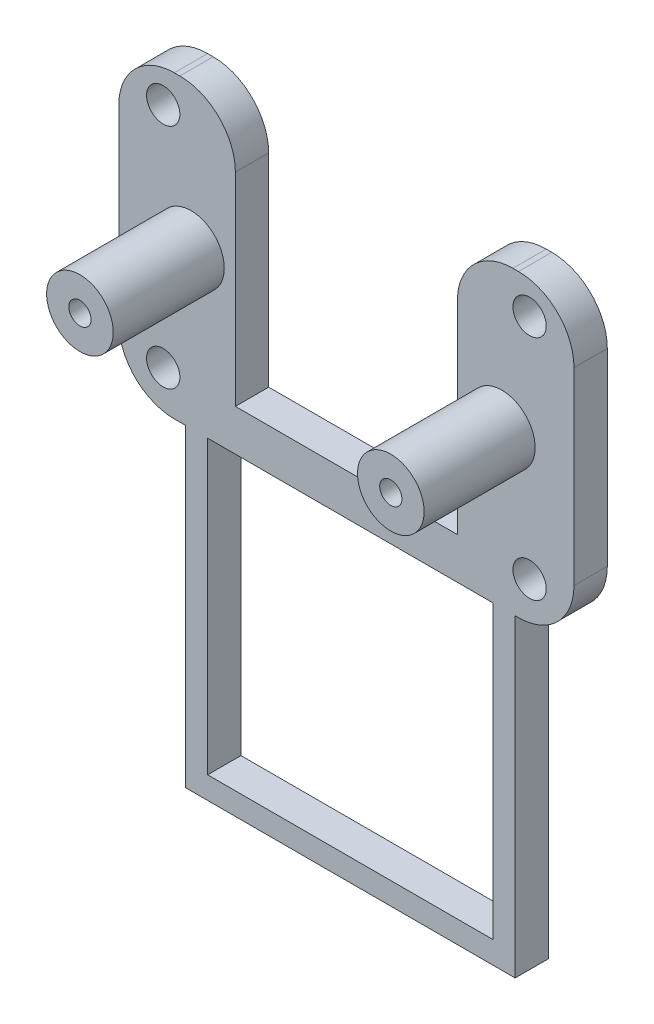
SolidWorks part; units mm, degrees
ref_plane "Plan de face" through (0, 0, 0) normal (0, 0, 1) x (1, 0, 0)
ref_plane "Plan de dessus" through (0, 0, 0) normal (0, 1, 0) x (1, 0, 0)
ref_plane "Plan de droite" through (0, 0, 0) normal (1, 0, 0) x (0, 0, -1)
sketch "Esquisse1" plane through (0, 0, 0) normal (0, 0, 1) x (1, 0, 0)
  line L0 (0, 0) -> (20.5, 0) construction
  line L1 (0, 0) -> (41, 0)
  line L2 (0, 0) -> (0, 27)
  line L3 (0, 27) -> (41, 27)
  line L4 (41, 0) -> (41, 27)
  line L5 (10.5, 3.7273) -> (30.5, 3.7273)
  line L6 (10.5, 3.7273) -> (10.5, 27.9545)
  line L7 (10.5, 27.9545) -> (30.5, 27.9545)
  line L8 (30.5, 3.7273) -> (30.5, 27.9545)
  line L9 (5.65, 0) -> (7.7004, 0)
  line L10 (5.65, 0) -> (35.35, 0)
  line L11 (7.65, 0) -> (33.35, 0)
  line L13 (7.65, 0) -> (33.35, 0)
  line L14 (7.65, 0) -> (16.0275, 0)
  line L17 (7.65, 0) -> (33.35, 0)
  line L23 (33.35, 0) -> (35.35, 0)
  line L24 (33.35, 0) -> (35.35, 0)
  circle A1 centre (4, 23.9981) radius 1.5
  circle A2 centre (4, 3.4981) radius 1.5
  circle A4 centre (37, 3.5002) radius 1.5
  circle A7 centre (37, 23.9983) radius 1.5
  dimension "D1" = 20.5
  dimension "D2" = 20.4981
  dimension "D3" = 33
  dimension "D5" = 3.5002
  dimension "D6" = 3.4981
  dimension "D7" = 10.5
  dimension "D9" = 20
extrude "Boss.-Extru.1" add sketch "Esquisse1" along normal blind 3 contours L8 L5 L6 L3 L2 L1 L4
sketch "Esquisse3" plane through (0, 0, 3) normal (0, 0, 1) x (1, 0, 0)
  line L0 (0, 0) -> (0, 27) construction
  line L1 (41, 0) -> (41, 27) construction
  line L2 (0, 0) -> (41, 0) construction
  circle A0 centre (6.5, 14) radius 1
  circle A1 centre (34.5, 14) radius 1
  circle A2 centre (6.5, 14) radius 3
  circle A3 centre (34.5, 14) radius 3
  dimension "D1" = 28
  dimension "D2" = 6.5
  dimension "D3" = 6.5
  dimension "D4" = 14
extrude "Boss.-Extru.2" add sketch "Esquisse3" along normal blind 10
fillet "Congé1" radius 5 6 edges at (41, 0, 1.5) (41, 27, 1.5) (30.5, 27, 1.5) (0, 0, 1.5) (10.5, 27, 1.5) (0, 27, 1.5)
sketch "Esquisse5" plane through (0, 0, 3) normal (0, 0, 1) x (1, 0, 0)
  line L0 (5, 0) -> (36, 0) construction
  line L1 (6, 0) -> (35.7, 0)
  line L2 (6, 0) -> (6, -28.26)
  line L3 (6, -28.26) -> (35.7, -28.26)
  line L4 (35.7, 0) -> (35.7, -28.26)
  line L5 (6, 0) -> (8, 0)
  line L6 (8, 0) -> (33.7, 0)
  line L7 (8, 0) -> (8, -26.26)
  line L8 (8, -26.26) -> (33.7, -26.26)
  line L9 (33.7, 0) -> (33.7, -26.26)
  line L10 (35.7, 0) -> (33.7, 0)
  line L11 (0, 5) -> (0, 22) construction
  line M7 (5, 0) -> (36, 0)
  dimension "D1" = 28.26
  dimension "D2" = 26.26
  dimension "D3" = 29.7
  dimension "D4" = 25.7
  dimension "D5" = 2
  dimension "D6" = 6
extrude "Boss.-Extru.3" add sketch "Esquisse5" against normal blind 3 contours L9 L8 L7 L2 L3 L4 M7
